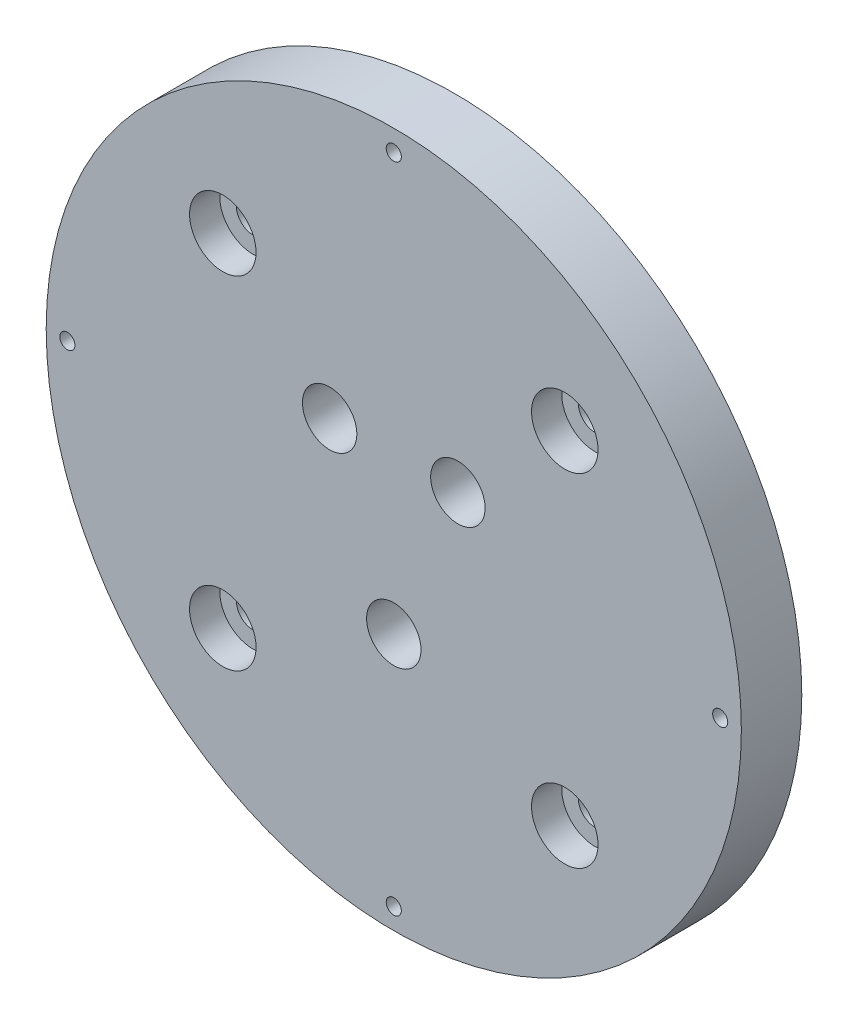
SolidWorks part; units mm, degrees
material "Malleable Cast Iron"
ref_plane "Front Plane" through (0, 0, 0) normal (0, 0, 1) x (1, 0, 0)
ref_plane "Top Plane" through (0, 0, 0) normal (0, 1, 0) x (1, 0, 0)
ref_plane "Right Plane" through (0, 0, 0) normal (1, 0, 0) x (0, 0, -1)
sketch "Sketch1" plane through (0, 0, 0) normal (0, 0, 1) x (1, 0, 0)
  circle A0 centre (0, 0) radius 57.5
  dimension "D1" = 115
extrude "Boss-Extrude1" add sketch "Sketch1" along normal blind 10
sketch "Sketch2" plane through (0, 0, 10) normal (0, 0, 1) x (1, 0, 0)
  line L0 (0, 0) -> (28.2843, 28.2843) construction
  line L1 (0, 0) -> (38.8683, 0) construction
  circle A0 centre (28.2843, 28.2843) radius 3
  dimension "D1" = 6
  dimension "D2" = 45
  dimension "D3" = 40
sketch "Sketch3" plane through (0, 0, 10) normal (0, 0, 1) x (1, 0, 0)
  line L0 (0, 0) -> (10.6066, 10.6066) construction
  line L1 (0, 0) -> (-10.6066, 10.6066) construction
  line L2 (0, 0) -> (0, -15) construction
  line L3 (0, 0) -> (24.3498, 0) construction
  circle A0 centre (0, -15) radius 4.5
  circle A1 centre (10.6066, 10.6066) radius 4.5
  circle A2 centre (-10.6066, 10.6066) radius 4.5
  dimension "D1" = 9
  dimension "D2" = 9
  dimension "D3" = 9
  dimension "D4" = 15
  dimension "D5" = 15
  dimension "D6" = 15
  dimension "D7" = 45
  dimension "D8" = 45
extrude "Cut-Extrude2" cut sketch "Sketch3" against normal blind 10
sketch "Sketch8" plane through (0, 0, 0) normal (0, 0, -1) x (-1, 0, 0)
  circle A0 centre (0, 0) radius 55
  circle A1 centre (0, 0) radius 53
  dimension "D1" = 110
  dimension "D2" = 106
extrude "Cut-Extrude6" cut sketch "Sketch8" against normal blind 1.27
hole_wizard "M3 Tapped Hole1" positions "Sketch9" profile "Sketch10" tap size "M3" standard "ISO"
sketch "Sketch9" plane through (0, 0, 10) normal (0, 0, 1) x (1, 0, 0)
  point P0 (0, 54)
  dimension "D1" = 54
sketch "Sketch10" plane through (0, 54, 10) normal (1, 0, 0) x (0, -1, 0)
  line L0 (0, 0) -> (0, 7.2511)
  line L1 (0, 7.2511) -> (1.25, 6.5)
  line L2 (1.25, 6.5) -> (1.25, 0)
  line L5 (1.25, 0) -> (0, 0)
  line L10 (0, 7.2511) -> (-1.25, 6.5) construction
  line L11 (0, -6.35) -> (0, 107.95) construction
  dimension "Tap Drill Dia." = 2.5
  dimension "Tap Drill Depth" = 6.5
  dimension "Drill Angle" = 118
cosmetic thread "Hole Thread1" parameters "D1"=5, "D2"=3
pattern_circular "CirPattern2" count 4 over 360 about axis through (0, 0, 0) along (0, 0, 1) of "M3 Tapped Hole1"
hole_wizard "Hole1" positions "Sketch11" profile "Sketch13" legacy
sketch "Sketch11" plane through (0, 0, 10) normal (0, 0, 1) x (1, 0, 0)
  point P0 (28.2843, 28.2843)
sketch "Sketch13" plane through (28.2843, 28.2843, 10) normal (1, 0, 0) x (0, -1, 0)
  line L0 (0, 0) -> (0, 10)
  line L1 (0, 10) -> (2.75, 10)
  line L2 (2.75, 10) -> (2.75, 5)
  line L3 (2.75, 5) -> (5.5, 5)
  line L4 (5.5, 5) -> (5.5, 0)
  line L5 (5.5, 0) -> (0, 0)
  line L6 (0, 110) -> (0, -10) construction
  dimension "Diameter" = 5.5
  dimension "Depth" = 10
  dimension "C-Bore Diameter" = 11
  dimension "C-Bore Depth" = 5
pattern_circular "CirPattern3" count 4 over 360 about axis through (0, 0, 0) along (0, 0, 1) of "Hole1"
